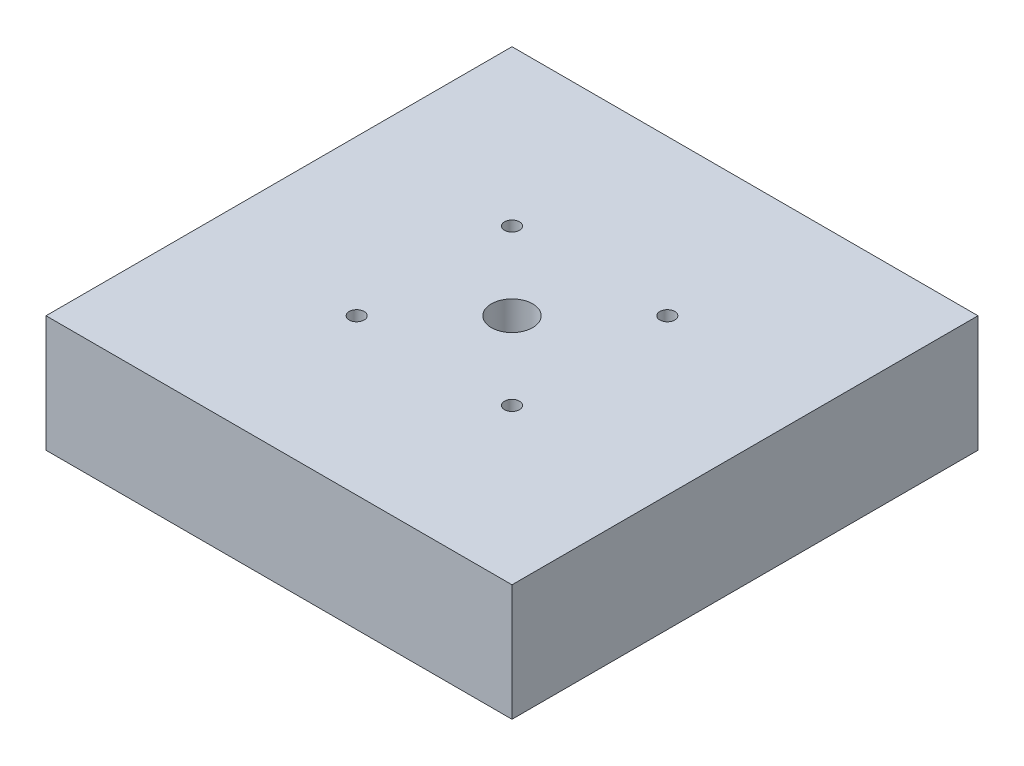
SolidWorks part; units mm, degrees
ref_plane "Front Plane" through (0, 0, 0) normal (0, 0, 1) x (1, 0, 0)
ref_plane "Top Plane" through (0, 0, 0) normal (0, 1, 0) x (1, 0, 0)
ref_plane "Right Plane" through (0, 0, 0) normal (1, 0, 0) x (0, 0, -1)
sketch "Sketch1" plane through (0, 0, 0) normal (0, 1, 0) x (1, 0, 0)
  line L1 (38.1, -38.1) -> (-38.1, -38.1)
  line L2 (38.1, -38.1) -> (38.1, 38.1)
  line L3 (38.1, 38.1) -> (-38.1, 38.1)
  line L4 (-38.1, -38.1) -> (-38.1, 38.1)
  line L5 (38.1, -38.1) -> (-38.1, 38.1) construction
  line L6 (38.1, 38.1) -> (-38.1, -38.1) construction
  point P0 (0, 0)
  dimension "D1" = 76.2
extrude "Boss-Extrude1" add sketch "Sketch1" along normal blind 19.05
hole_wizard "1/4 Clearance Hole1" positions "Sketch2" profile "Sketch3" hole size "1/4" standard "ANSI Inch" end condition through all
sketch "Sketch2" plane through (0, 19.05, 0) normal (0, 1, 0) x (1, 0, 0)
  point P0 (0, 0)
sketch "Sketch3" plane through (0, 19.05, 0) normal (1, 0, 0) x (0, 0, 1)
  line L0 (0, 0) -> (0, 19.05)
  line L1 (0, 19.05) -> (3.3782, 19.05)
  line L2 (3.3782, 19.05) -> (3.3782, 0)
  line L3 (3.3782, 0) -> (0, 0)
  line L4 (0, -6.35) -> (0, 107.95) construction
  dimension "Thru Hole Dia." = 6.7564
  dimension "Thru Hole Depth" = 19.05
hole_wizard "#2 Clearance Hole1" positions "Sketch4" profile "Sketch5" hole size "#2" standard "ANSI Inch" end condition through all
sketch "Sketch4" plane through (0, 19.05, 0) normal (0, 1, 0) x (1, 0, 0)
  line L1 (12.7, -12.7) -> (-12.7, -12.7)
  line L2 (12.7, -12.7) -> (12.7, 12.7)
  line L3 (12.7, 12.7) -> (-12.7, 12.7)
  line L4 (-12.7, -12.7) -> (-12.7, 12.7)
  line L5 (12.7, -12.7) -> (-12.7, 12.7) construction
  line L6 (12.7, 12.7) -> (-12.7, -12.7) construction
  point P0 (-12.7, 12.7)
  point P3 (0, 0)
sketch "Sketch5" plane through (-12.7, 19.05, -12.7) normal (1, 0, 0) x (0, 0, 1)
  line L0 (0, 0) -> (0, 19.05)
  line L1 (0, 19.05) -> (1.2192, 19.05)
  line L2 (1.2192, 19.05) -> (1.2192, 0)
  line L3 (1.2192, 0) -> (0, 0)
  line L4 (0, -6.35) -> (0, 107.95) construction
  dimension "Thru Hole Dia." = 2.4384
  dimension "Thru Hole Depth" = 19.05
hole_wizard "#2 Clearance Hole2" positions "Sketch6" profile "Sketch7" hole size "#2" standard "ANSI Inch" end condition through all
sketch "Sketch6" plane through (0, 19.05, 0) normal (0, 1, 0) x (1, 0, 0)
  point P0 (12.7, 12.7)
  point P1 (-12.7, -12.7)
  point P2 (12.7, -12.7)
sketch "Sketch7" plane through (12.7, 19.05, -12.7) normal (1, 0, 0) x (0, 0, 1)
  line L0 (0, 0) -> (0, 19.05)
  line L1 (0, 19.05) -> (1.2192, 19.05)
  line L2 (1.2192, 19.05) -> (1.2192, 0)
  line L3 (1.2192, 0) -> (0, 0)
  line L4 (0, -6.35) -> (0, 107.95) construction
  dimension "Thru Hole Dia." = 2.4384
  dimension "Thru Hole Depth" = 19.05
equation "\".hf\"=0.1"
